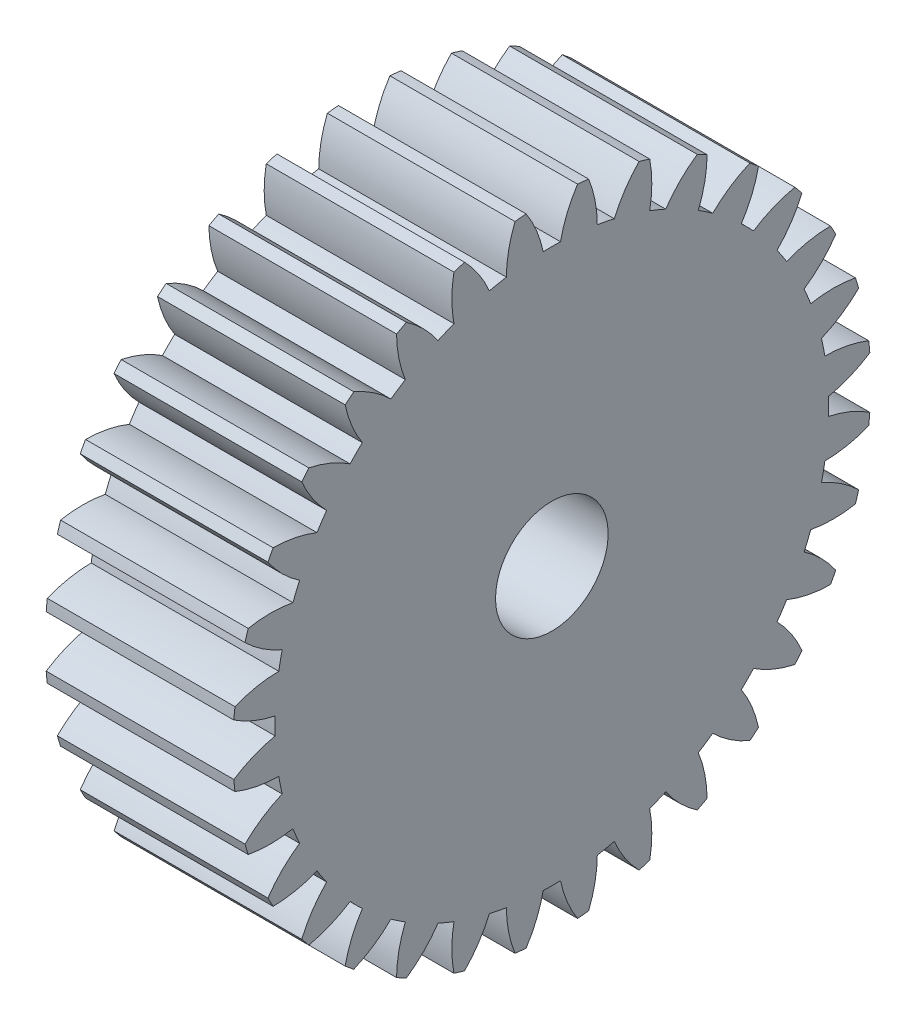
SolidWorks part; units mm, degrees
ref_plane "Plane1" through (0, 0, 0) normal (0, 0, 1) x (1, 0, 0)
ref_plane "Plane2" through (0, 0, 0) normal (0, 1, 0) x (1, 0, 0)
ref_plane "Plane3" through (0, 0, 0) normal (1, 0, 0) x (0, 0, -1)
other "Configuration Table"
sketch "HoldingSke" plane through (0, 0, 0) normal (0, 1, 0) x (1, 0, 0)
  line L0 (0, 0) -> (0.848, -0.5299)
  line L1 (-15, 0) -> (100, 0) construction
  line L2 (0, 0) -> (-2.1039, 2.3779)
  line L3 (0, 0) -> (-11.863, 4.5341)
  line L4 (0, 0) -> (7.3237, 4.5764)
  line L5 (0, 0) -> (-46.8476, -17.4728)
  line L6 (0, 0) -> (-8.2896, -5.593)
  line L7 (-2.1039, 2.3779) -> (8.6586, 51.2059)
  line L8 (-76.2, 54.61) -> (-75.2, 54.61)
  line L9 (-71.009, 38.7566) -> (-53.1078, 45.2721)
  line L10 (-76.2, 71.12) -> (104.1128, 71.12)
  line L11 (0, 0) -> (-10, 0)
  line L12 (-76.2, 101.6) -> (-76.162, 101.6)
  line L13 (24.9733, 27.94) -> (52.9518, 28.4284)
  line L14 (24.9733, 27.94) -> (24.9743, 27.94)
  line L15 (24.9733, 27.94) -> (100.4006, 29.5858)
  line L16 (-63.627, -1) -> (-12.827, -1)
  circle A0 centre (0, 0) radius 3
  circle A1 centre (0, 0) radius 14.749
  circle A2 centre (0, 0) radius 37.5
  circle A3 centre (0, 0) radius 3
  dimension "MHD" = 29.498
  dimension "Hub_dia" = 75
  dimension "Bore" = 6
  dimension "MBD" = 6
  dimension "Num_teeth" = 32
  dimension "Pitch" = 1
  dimension "Overall_len" = 50
  dimension "Show_teeth" = 32
  dimension "Thickness" = 10
  dimension "OAL" = 50.0001
  dimension "T_dim" = 1
  dimension "Ap" = 20
  dimension "H" = 19.05
  dimension "Pitch_radius" = 180.3128
  dimension "Width" = 10
  dimension "Backlash" = 0.038
  dimension "Addendum_fac" = 1
  dimension "Dedendum_fac" = 1.25
  dimension "Clearance_fac" = 0.25
  dimension "Dedendum_add" = 0.001
  dimension "Module" = 1
sketch "BasProSke" plane through (0, 0, 0) normal (0, 1, 0) x (1, 0, 0)
  line L0 (-10, 0) -> (60, 0) construction
  line L1 (0, 0) -> (0, 17)
  line L2 (0, 0) -> (10, 0)
  line L3 (10, 0) -> (10, 17)
  line L4 (10, 17) -> (0, 17)
  dimension "Thickness" = 10
  dimension "Diameter" = 34
revolve "Base-Revolve" add sketch "BasProSke" angle 360 about L0
sketch "TooCutSke" plane through (0, 0, 0) normal (1, 0, 0) x (0, 0, -1)
  line L1 (0, 0) -> (0, 107) construction
  line L2 (0, 0) -> (-0.8516, 15.9773) construction
  line L3 (0, 0) -> (-3.1334, 31.8138) construction
  line L4 (-0.8516, 15.9773) -> (-1.5667, 15.9069) construction
  arc A0 (0.462, 14.7418) -> (-0.462, 14.7418) centre (0, 0) ccw
  arc A1 (1.3867, 16.9688) -> (-1.3867, 16.9688) centre (0, 0) ccw
  circle A2 centre (0, 0) radius 16 construction
  circle A3 centre (0, 0) radius 15.0351 construction
  arc A4 (-0.462, 14.7418) -> (-1.3867, 16.9688) centre (-6.7293, 13.4451) ccw
  arc A5 (1.3867, 16.9688) -> (0.462, 14.7418) centre (6.7293, 13.4451) ccw
  dimension "Root_dia" = 29.498
  dimension "Overcut_dia" = 34.0508
  dimension "Pitch_dia" = 32
  dimension "Base_dia" = 30.0702
  dimension "Flank_rad" = 6.4
  dimension "Half_ang" = 5.625
  dimension "Half_CT" = 0.7186
extrude "ToothCut" cut sketch "TooCutSke" along normal through all
fillet "Breaks" [suppressed] radius 0.02
fillet "RootFillets" [suppressed] radius 0.251
pattern_circular "TeethCuts" count 32 every 11.25 about axis through (-10, 0, 0) along (1, 0, 0) of "ToothCut", "RootFillets", "Breaks"
sketch "HubNeaOneSke" plane through (0, 0, 0) normal (-1, 0, 0) x (0, 0, 1)
  circle A0 centre (0, 0) radius 14.749
  dimension "Diameter" = 29.498
extrude "HubNearOne" [suppressed] add sketch "HubNeaOneSke" along normal blind 40.0001
sketch "HubNeaBotSke" plane through (0, 0, 0) normal (-1, 0, 0) x (0, 0, 1)
  circle A0 centre (0, 0) radius 14.749
  dimension "Diameter" = 29.498
extrude "HubNearBoth" [suppressed] add sketch "HubNeaBotSke" along normal blind 20
ref_plane "FarPln" through (10, 0, 0) normal (1, 0, 0) x (0, 0, -1)
sketch "HubFarSke" plane through (10, 0, 0) normal (1, 0, 0) x (0, 0, -1)
  circle A0 centre (0, 0) radius 14.749
  dimension "Diameter" = 29.498
extrude "HubFar" [suppressed] add sketch "HubFarSke" along normal blind 20
sketch "BorSke" plane through (0, 0, 0) normal (1, 0, 0) x (0, 0, -1)
  circle A0 centre (0, 0) radius 3
  dimension "Diameter" = 6
extrude "Bore" cut sketch "BorSke" along normal mid plane 100.0001
sketch "KeySke" plane through (0, 0, 0) normal (1, 0, 0) x (0, 0, -1)
  line L0 (-1, 0) -> (-1, 4)
  line L1 (-1, 4) -> (1, 4)
  line L2 (1, 4) -> (1, 0)
  line L3 (0, 0) -> (0, 34) construction
  line L4 (-1, 0) -> (1, 0)
  dimension "Offset" = 4
  dimension "Width" = 2
extrude "Keyway" [suppressed] cut sketch "KeySke" along normal mid plane 100.0001
pattern_circular "Keyway2" [suppressed] count 2 every 90 about axis through (-10, 0, 0) along (1, 0, 0)
equation "' \"Module@HoldingSke\" = 6.35"
equation "' \"Num_teeth@HoldingSke\" = 12"
equation "' \"Ap@HoldingSke\" =  20"
equation "' \"Ap@HoldingSke\" = 20"
equation "' \"Width@HoldingSke\" = 0.5 * 25.4"
equation "' \"Hub_dia@HoldingSke\"= 1 * 25.4"
equation "' \"Hub_dia@HoldingSke\" = 1 * 25.4"
equation "' \"Overall_len@HoldingSke\" = 1.0 * 25.4"
equation "' \"Bore@HoldingSke\" = 0.75 * 25.4"
equation "' \"T_dim@HoldingSke\" = 0.1 * 25.4"
equation "' \"Width@KeySke\" = 0.25 * 25.4"
equation "' \"Show_teeth@HoldingSke\" = 13"
equation "' \"Backlash@HoldingSke\" = 0.009 * 25.4"
equation "' \"Addendum_fac@HoldingSke\" = 1.0"
equation "' \"Dedendum_fac@HoldingSke\" = 1.25"
equation "' \"Dedendum_add@HoldingSke\" = 0.00005 * 25.4"
equation "' \"Clearance_fac@HoldingSke\" = 0.25"
equation "\"Pitch@HoldingSke\" = 1 / \"Module@HoldingSke\""
equation "\"Overcut_dia@TooCutSke\" = (\"Num_teeth@HoldingSke\" + 2 * \"Addendum_fac@HoldingSke\") / \"Pitch@HoldingSke\" + 0.002 * 25.4"
equation "\"Pitch_dia@TooCutSke\" = \"Num_teeth@HoldingSke\" / \"Pitch@HoldingSke\""
equation "\"Base_dia@TooCutSke\" = \"Num_teeth@HoldingSke\" / \"Pitch@HoldingSke\" * cos((\"Ap@HoldingSke\"  * 3.14159265 / 180))"
equation "\"Root_dia@TooCutSke\" = (\"Num_teeth@HoldingSke\" + 2) / \"Pitch@HoldingSke\" - 2 * (\"Addendum_fac@HoldingSke\" + \"Dedendum_fac@HoldingSke\") / \"Pitch@HoldingSke\" - \"Dedendum_add@HoldingSke\" * 2"
equation "\"Half_ang@TooCutSke\" = 180 / \"Num_teeth@HoldingSke\""
equation "\"Half_CT@TooCutSke\" = \"Num_teeth@HoldingSke\" / \"Pitch@HoldingSke\" * sin((3.14159265 / 2 / \"Num_teeth@HoldingSke\")) / 2 - 7 * \"Backlash@HoldingSke\" / 4"
equation "\"Flank_rad@TooCutSke\" = \"Num_teeth@HoldingSke\" / \"Pitch@HoldingSke\" / 5"
equation "\"Radius@RootFillets\" = \"Clearance_fac@HoldingSke\" / \"Pitch@HoldingSke\" + \"Dedendum_add@HoldingSke\""
equation "\"Break_rad@Breaks\" = 0.02 / \"Pitch@HoldingSke\""
equation "\"Thickness@HoldingSke\" = \"Width@HoldingSke\""
equation "\"OAL@HoldingSke\" = \"Thickness@HoldingSke\""
equation "\"MHD@HoldingSke\" = (\"Num_teeth@HoldingSke\" + 2) / \"Pitch@HoldingSke\" - 2 * (\"Addendum_fac@HoldingSke\" + \"Dedendum_fac@HoldingSke\")  / \"Pitch@HoldingSke\" - \"Dedendum_add@HoldingSke\" * 2"
equation "\"MBD@HoldingSke\" = (\"Num_teeth@HoldingSke\" + 2) / \"Pitch@HoldingSke\" - 2 * (\"Addendum_fac@HoldingSke\" + \"Dedendum_fac@HoldingSke\")  / \"Pitch@HoldingSke\" - \"Dedendum_add@HoldingSke\" * 2 - 0.002 * 25.4"
equation "\"MHD@HoldingSke\" = ((sgn( \"MHD@HoldingSke\" - \"Hub_dia@HoldingSke\" )-1)*( \"MHD@HoldingSke\" - \"Hub_dia@HoldingSke\" ))/-2+ \"Hub_dia@HoldingSke\""
equation "\"MBD@HoldingSke\" = ((sgn( \"MBD@HoldingSke\" - \"Bore@HoldingSke\" )-1)*( \"MBD@HoldingSke\" - \"Bore@HoldingSke\" ))/-2+ \"Bore@HoldingSke\""
equation "\"OAL@HoldingSke\" = ((sgn( \"OAL@HoldingSke\" - \"Overall_len@HoldingSke\" )+1)*( \"OAL@HoldingSke\" - \"Overall_len@HoldingSke\" ))/2 + \"Overall_len@HoldingSke\" + 0.000002 * 25.4"
equation "\"Num_teeth@TeethCuts\" = int( \"Show_teeth@HoldingSke\" ) + 1"
equation "\"Num_teeth@TeethCuts\" = ((sgn( \"Num_teeth@TeethCuts\" - \"Num_teeth@HoldingSke\" )-1)*( \"Num_teeth@TeethCuts\" - \"Num_teeth@HoldingSke\" ))/-2+ \"Num_teeth@HoldingSke\""
equation "\"Num_teeth@TeethCuts\" = ((sgn( \"Num_teeth@TeethCuts\" - 2.0)+1)*( \"Num_teeth@TeethCuts\" - 2.0))/2 +2.0"
equation "\"Angle@TeethCuts\" = 360.0 / \"Num_teeth@HoldingSke\""
equation "\"Diameter@BasProSke\" = (\"Num_teeth@HoldingSke\" + 2 * \"Addendum_fac@HoldingSke\") / \"Pitch@HoldingSke\""
equation "\"Thickness@BasProSke\"  = \"Thickness@HoldingSke\""
equation "' \"Fillet_rad@BasProSke\" =  \"Thickness@HoldingSke\" * 0.05"
equation "' \"Fillet_rad@BasProSke\" = \"Thickness@HoldingSke\" * 0.05"
equation "\"MHD@HoldingSke\" = ((sgn( \"MHD@HoldingSke\" - \"Root_dia@TooCutSke\" )-1)*( \"MHD@HoldingSke\" - \"Root_dia@TooCutSke\" ))/-2+ \"Root_dia@TooCutSke\""
equation "\"Diameter@HubNeaOneSke\" = \"MHD@HoldingSke\""
equation "\"Length@HubNearOne\" = \"OAL@HoldingSke\" - \"Thickness@BasProSke\""
equation "\"Diameter@HubNeaBotSke\" = \"MHD@HoldingSke\""
equation "\"Length@HubNearBoth\" = ( \"OAL@HoldingSke\" - \"Thickness@BasProSke\" ) / 2.0"
equation "\"Thickness@FarPln\" = \"Thickness@BasProSke\""
equation "\"Diameter@HubFarSke\" = \"MHD@HoldingSke\""
equation "\"Length@HubFar\" = ( \"OAL@HoldingSke\" - \"Thickness@BasProSke\" ) / 2.0"
equation "\"Diameter@BorSke\" = \"MBD@HoldingSke\""
equation "\"D1@Bore\" = \"OAL@HoldingSke\" * 2.0"
equation "\"D1@Keyway\" = \"OAL@HoldingSke\" * 2.0"
equation "\"Offset@KeySke\" = \"T_dim@HoldingSke\" + \"MBD@HoldingSke\" / 2.0"
